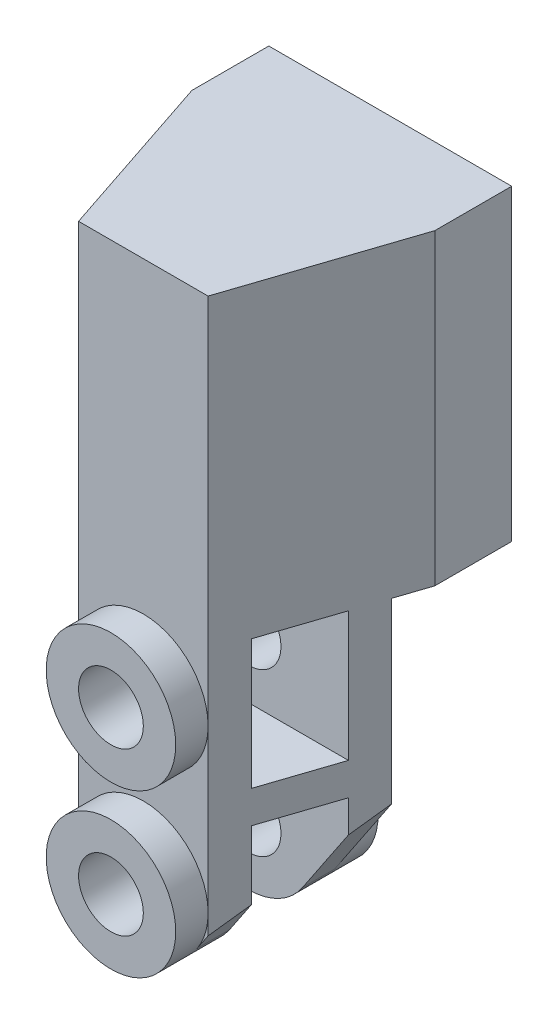
SolidWorks part; units mm, degrees
ref_plane "Front" through (0, 0, 0) normal (0, 0, 1) x (1, 0, 0)
ref_plane "Top" through (0, 0, 0) normal (0, 1, 0) x (1, 0, 0)
ref_plane "Right" through (0, 0, 0) normal (1, 0, 0) x (0, 0, -1)
sketch "Sketch1" plane through (0, 0, 0) normal (0, 0, 1) x (1, 0, 0)
  line L0 (-11.9062, 0) -> (11.9062, 0)
  line L1 (-11.9062, 0) -> (-11.9062, -25.4)
  line L2 (-11.9062, -25.4) -> (11.9062, -25.4) construction
  line L3 (11.9062, -25.4) -> (11.9062, 0)
  line L4 (11.9062, -25.4) -> (11.9062, -58.7375)
  line L5 (11.9062, -58.7375) -> (-11.9062, -58.7375)
  line L6 (-11.9062, -58.7375) -> (-11.9062, -25.4)
  dimension "D1" = 23.8125
  dimension "D2" = 25.4
  dimension "D3" = 33.3375
extrude "Boss-Extrude1" add sketch "Sketch1" along normal blind 24.2094
sketch "Sketch2" plane through (0, -58.7375, 0) normal (0, -1, 0) x (1, 0, 0)
  line L0 (-11.9062, 0) -> (-11.9062, 7.5406) construction
  line L1 (-11.9062, 24.2094) -> (-11.9062, 0) construction
  line L2 (-11.9062, 7.5406) -> (-6.35, 24.2094)
  line L3 (-11.9062, 24.2094) -> (11.9062, 24.2094) construction
  line L4 (-6.35, 24.2094) -> (6.35, 24.2094)
  line L5 (6.35, 24.2094) -> (11.9062, 7.5406)
  line L6 (11.9062, 24.2094) -> (11.9062, 0) construction
  line L7 (-11.9062, 7.5406) -> (-11.9062, 24.2094)
  line L8 (-11.9062, 24.2094) -> (-6.35, 24.2094)
  line L9 (11.9062, 7.5406) -> (11.9062, 24.2094)
  line L10 (11.9062, 24.2094) -> (6.35, 24.2094)
  line L11 (-11.9062, 7.5406) -> (11.9062, 7.5406) construction
  line L12 (-11.9062, 0) -> (11.9062, 0) construction
  line M7 (11.9062, 0) -> (11.9062, 24.2094)
  line M8 (11.9062, 24.2094) -> (-11.9062, 24.2094)
  line M9 (-11.9062, 24.2094) -> (-11.9062, 0)
  dimension "D1" = 12.7
  dimension "D2" = 7.5406
extrude "Cut-Extrude1" cut sketch "Sketch2" against normal through all contours L2 M9 M8 | L5 M8 M7
sketch "Sketch3" plane through (0, 0, 24.2094) normal (0, 0, 1) x (1, 0, 0)
  line L0 (-6.35, -58.7375) -> (6.35, -58.7375) construction
  line L1 (6.35, 0) -> (6.35, -58.7375) construction
  line L2 (-6.35, 0) -> (-6.35, -58.7375) construction
  line L3 (5.2734, -55.925) -> (11.9062, -46.0375)
  line L4 (11.9062, 0) -> (11.9062, -58.7375) construction
  line L5 (11.9062, -46.0375) -> (11.9062, -58.7375)
  line L6 (11.9062, -58.7375) -> (0, -58.7375)
  line L7 (0, -58.7375) -> (-11.9062, -58.7375)
  line L8 (-11.9062, -58.7375) -> (-11.9062, -46.0375)
  line L9 (-11.9062, 0) -> (-11.9062, -58.7375) construction
  line L10 (-11.9062, -46.0375) -> (-5.2734, -55.925)
  line L11 (-11.9062, -46.0375) -> (11.9062, -46.0375) construction
  arc A0 (-5.2734, -55.925) -> (5.2734, -55.925) centre (0, -52.3875) ccw
  arc A1 (5.2734, -55.925) -> (0, -46.0375) centre (0, -52.3875) ccw construction
  arc A2 (0, -46.0375) -> (-5.2734, -55.925) centre (0, -52.3875) ccw construction
  line M5 (-6.35, 0) -> (-6.35, -58.7375)
  line M6 (-6.35, -58.7375) -> (6.35, -58.7375)
  line M7 (6.35, -58.7375) -> (6.35, 0)
extrude "Cut-Extrude2" cut sketch "Sketch3" against normal through all contours L10 L8 L7 M5 | L6 L5 L3 M7 | A0 L3 M6 M7 | A0 L10 M5 M6
sketch "Sketch4" plane through (0, 0, 24.2094) normal (0, 0, 1) x (1, 0, 0)
  circle A0 centre (0, -52.3875) radius 3.175
  arc A1 (-5.2734, -55.925) -> (5.2734, -55.925) centre (0, -52.3875) ccw construction
  circle A2 centre (0, -36.5125) radius 3.175
  point P7 (1.1317, -36.5529)
  dimension "D1" = 6.35
  dimension "D2" = 15.875
extrude "Cut-Extrude3" cut sketch "Sketch4" against normal through all
sketch "Sketch5" plane through (0, 0, 0) normal (1, 0, 0) x (0, 0, -1)
  line L0 (-24.2094, -58.7375) -> (0, -58.7375) construction
  line L1 (-13.8906, -46.0375) -> (-21.0344, -46.0375)
  line L2 (-13.8906, -46.0375) -> (-13.8906, -58.7375)
  line L3 (-13.8906, -58.7375) -> (-21.0344, -58.7375)
  line L4 (-21.0344, -46.0375) -> (-21.0344, -58.7375)
  line L5 (-21.0344, -52.3875) -> (-24.2094, -52.3875) construction
  line L6 (-24.2094, 0) -> (-24.2094, -54.3201) construction
  line L7 (-17.4625, -42.8625) -> (-17.4625, -46.0375) construction
  line L8 (-13.8906, -42.8625) -> (-21.0344, -42.8625)
  line L9 (-13.8906, -42.8625) -> (-13.8906, -30.1625)
  line L10 (-13.8906, -30.1625) -> (-21.0344, -30.1625)
  line L11 (-21.0344, -42.8625) -> (-21.0344, -30.1625)
  line L12 (-13.8906, -42.8625) -> (-13.8906, -46.0375) construction
  line L13 (-10.7156, -30.1625) -> (0, -30.1625)
  line L14 (-10.7156, -30.1625) -> (-10.7156, -58.7375)
  line L15 (-10.7156, -58.7375) -> (0, -58.7375)
  line L16 (0, -30.1625) -> (0, -58.7375)
  line L17 (-10.7156, -44.45) -> (-13.8906, -44.45) construction
  dimension "D1" = 3.175
  dimension "D2" = 7.1437
  dimension "D3" = 12.7
extrude "Cut-Extrude4" cut sketch "Sketch5" against normal through all both and the other way through all
sketch "Sketch6" plane through (0, 0, 24.2094) normal (0, 0, 1) x (1, 0, 0)
  line L0 (6.35, 0) -> (6.35, -54.3201) construction
  circle A0 centre (0, -36.5125) radius 6.35
  circle A1 centre (0, -52.3875) radius 6.35
  arc A2 (-5.2734, -55.925) -> (5.2734, -55.925) centre (0, -52.3875) ccw construction
  circle A3 centre (0, -52.3875) radius 3.175 construction
  circle A4 centre (0, -36.5125) radius 3.175 construction
  circle A5 centre (0, -52.3875) radius 3.175
  circle A6 centre (0, -36.5125) radius 3.175
extrude "Boss-Extrude2" add sketch "Sketch6" along normal blind 3.175
sketch "Sketch7" plane through (0, 0, 10.7156) normal (0, 0, -1) x (-1, 0, 0)
  line L0 (-3.175, -30.1625) -> (-3.175, -31.0132)
  line L1 (10.8479, -30.1625) -> (-10.8479, -30.1625) construction
  line L2 (3.175, -30.1625) -> (3.175, -31.0132)
  line L3 (-3.175, -30.1625) -> (3.175, -30.1625)
  line L4 (0, -30.1625) -> (0, -36.5125) construction
  circle A0 centre (0, -52.3875) radius 6.35 construction
  circle A1 centre (0, -36.5125) radius 6.35 construction
  circle A2 centre (0, -52.3875) radius 6.35
  arc A3 (-3.175, -31.0132) -> (3.175, -31.0132) centre (0, -36.5125) ccw
  arc A4 (0, -30.1625) -> (-3.175, -31.0132) centre (0, -36.5125) ccw construction
  arc A5 (3.175, -31.0132) -> (0, -30.1625) centre (0, -36.5125) ccw construction
  circle A6 centre (0, -36.5125) radius 3.175 construction
  circle A7 centre (0, -36.5125) radius 3.175
  circle A8 centre (0, -52.3875) radius 3.175 construction
  circle A9 centre (0, -52.3875) radius 3.175
  dimension "D1" = 6.35
extrude "Boss-Extrude4" add sketch "Sketch7" along normal blind 3.175
